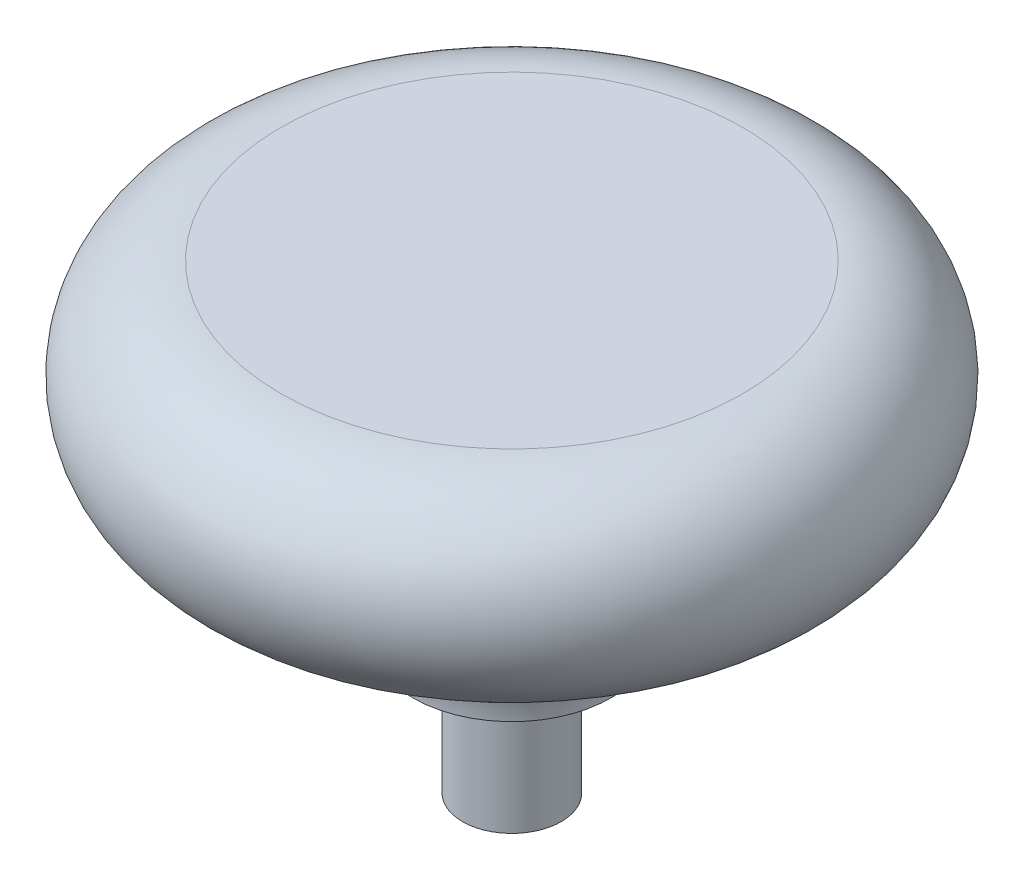
SolidWorks part; units mm, degrees
ref_plane "Front Plane" through (0, 0, 0) normal (0, 0, 1) x (1, 0, 0)
ref_plane "Top Plane" through (0, 0, 0) normal (0, 1, 0) x (1, 0, 0)
ref_plane "Right Plane" through (0, 0, 0) normal (1, 0, 0) x (0, 0, -1)
sketch "Sketch1" plane through (0, 0, 0) normal (0, 0, 1) x (1, 0, 0)
  line L0 (-81.6716, 0) -> (68.3102, 0) construction
  line L1 (0, 36.6604) -> (0, 0) construction
  line L2 (11.12, 11.11) -> (0, 11.11)
  line L5 (0, 11.11) -> (0, -11.11)
  line L6 (0, -11.11) -> (2.38, -11.11)
  line L7 (2.38, -11.11) -> (2.38, -4.76)
  line L8 (2.38, -4.76) -> (4.765, -4.76)
  arc A3 (11.12, 1.59) -> (11.12, 11.11) centre (11.12, 6.35) ccw
  arc A4 (4.765, -4.76) -> (11.12, 1.59) centre (11.115, -4.76) cw
  point P13 (0, 0)
  point P14 (0, 0)
  dimension "D1" = 9.52
  dimension "D3" = 22.22
  dimension "D5" = 2.385
  dimension "D6" = 6.35
  dimension "D7" = 6.35
  dimension "D2" = 11.12
  dimension "D4" = 2.38
revolve "Revolve1" add sketch "Sketch1" angle 360 about L1
